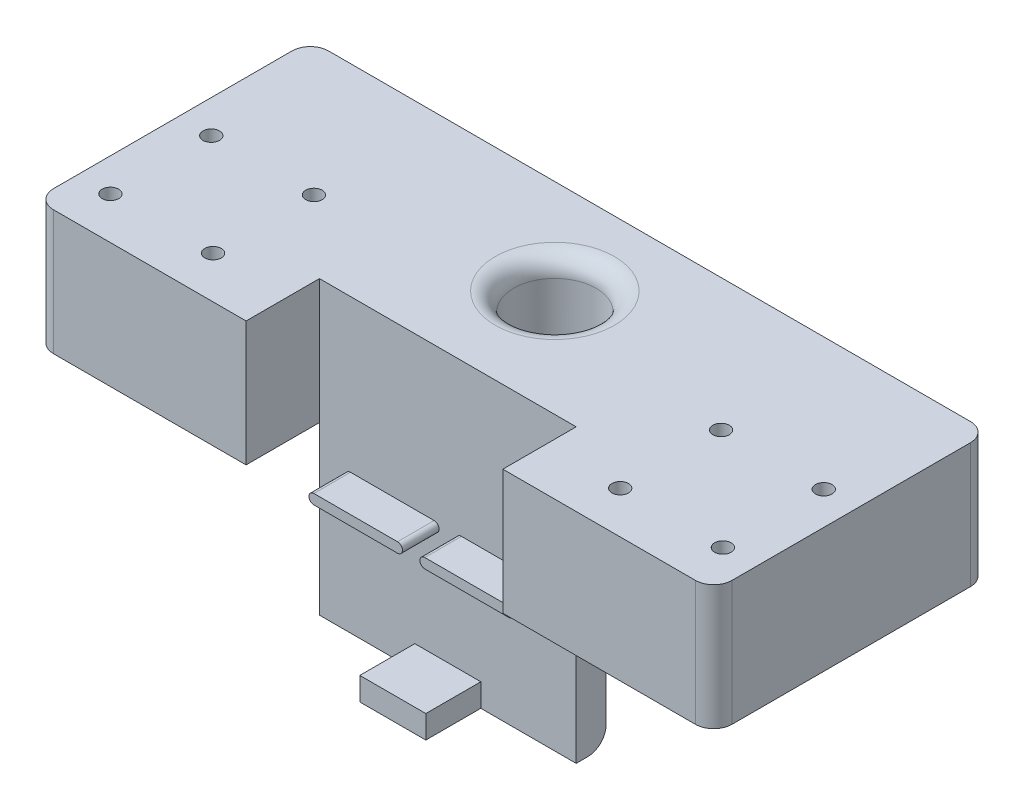
SolidWorks part; units mm, degrees
ref_plane "Front Plane" through (0, 0, 0) normal (0, 0, 1) x (1, 0, 0)
ref_plane "Top Plane" through (0, 0, 0) normal (0, 1, 0) x (1, 0, 0)
ref_plane "Right Plane" through (0, 0, 0) normal (1, 0, 0) x (0, 0, -1)
ref_plane "Plane1" through (0, -15, 0) normal (0, -1, 0) x (1, 0, 0)
sketch "Sketch1" plane through (0, -15, 0) normal (0, -1, 0) x (1, 0, 0)
  line L0 (-92.5, 0) -> (92.5, 0)
  line L1 (92.5, 0) -> (92.5, 55)
  line L2 (92.5, 55) -> (-92.5, 55)
  line L3 (-92.5, 55) -> (-92.5, 0)
extrude "Boss-Extrude1" add sketch "Sketch1" against normal blind 49
sketch "Sketch2" plane through (0, 0, 55) normal (0, 0, 1) x (1, 0, 0)
  line L0 (26.525, -10.2) -> (3.725, -10.2)
  line L1 (3.725, -7.5) -> (26.525, -7.5)
  line L2 (92.5, 34) -> (-92.5, 34) construction
  arc A0 (26.525, -7.5) -> (26.525, -10.2) centre (26.525, -8.85) cw
  arc A1 (3.725, -10.2) -> (3.725, -7.5) centre (3.725, -8.85) cw
  dimension "D1" = 41.5
extrude "Boss-Extrude2" add sketch "Sketch2" along normal blind 10
sketch "Sketch3" plane through (0, -10.2, 0) normal (0, -1, 0) x (1, 0, 0)
  line L0 (17.9948, 65) -> (0, 65)
  line L1 (0, 65) -> (0, 56.75)
  arc A0 (0, 56.75) -> (17.9948, 65) centre (0, 80.5) ccw
sketch "Sketch4" plane through (0, 0, 0) normal (0, 0, -1) x (-1, 0, 0)
  line L0 (-35, -15) -> (-35, 0)
  line L1 (-35, 0) -> (-92.5, 0)
  line L2 (-92.5, 0) -> (-92.5, -15)
  line L3 (-92.5, -15) -> (-35, -15)
extrude "Cut-Extrude2" cut sketch "Sketch4" against normal through all
sketch "Sketch5" plane through (0, 0, 55) normal (0, 0, 1) x (1, 0, 0)
  line L0 (-92.5, -15) -> (-35, -15)
  line L1 (-35, -15) -> (-35, 0)
  line L2 (-35, 0) -> (-92.5, 0)
  line L3 (-92.5, 0) -> (-92.5, -15)
extrude "Cut-Extrude3" cut sketch "Sketch5" against normal through all
sketch "Sketch6" plane through (0, 0, 55) normal (0, 0, 1) x (1, 0, 0)
  line L0 (-26.525, -7.5) -> (-3.725, -7.5)
  line L1 (-3.725, -10.2) -> (-26.525, -10.2)
  line L2 (92.5, 34) -> (-92.5, 34) construction
  arc A0 (-26.525, -10.2) -> (-26.525, -7.5) centre (-26.525, -8.85) cw
  arc A1 (-3.725, -7.5) -> (-3.725, -10.2) centre (-3.725, -8.85) cw
  dimension "D1" = 41.5
extrude "Boss-Extrude3" add sketch "Sketch6" along normal blind 10
sketch "Sketch7" plane through (0, -7.5, 0) normal (0, 1, 0) x (-1, 0, 0)
  line L0 (17.9948, 65) -> (-0.1994, 65)
  line L1 (-0.1994, 65) -> (-0.1994, 56.7508)
  arc A0 (-0.1994, 56.7508) -> (17.9948, 65) centre (0, 80.5) ccw
sketch "Sketch8" plane through (0, 0, 0) normal (0, 0, -1) x (-1, 0, 0)
  line L0 (-11.45, 16.55) -> (11.45, 16.55)
  line L1 (11.45, 13.95) -> (-11.45, 13.95)
  line L2 (92.5, 34) -> (-92.5, 34) construction
  line L3 (-35, -7.5) -> (35, -7.5) construction
  line L4 (-35, -15) -> (-35, 0) construction
  line L5 (35, -15) -> (35, 0) construction
  arc A0 (11.45, 16.55) -> (11.45, 13.95) centre (11.45, 15.25) cw
  arc A1 (-11.45, 13.95) -> (-11.45, 16.55) centre (-11.45, 15.25) cw
  dimension "D1" = 22.75
  dimension "D2" = 41.5
  dimension "D3" = 2.6
extrude "Boss-Extrude4" add sketch "Sketch8" along normal blind 3.5
sketch "Sketch10" plane through (0, 0, 0) normal (0, 0, -1) x (-1, 0, 0)
  line L0 (-18.55, 13.95) -> (-42.45, 13.95)
  line L1 (-42.45, 16.55) -> (-18.55, 16.55)
  line L2 (92.5, 34) -> (-92.5, 34) construction
  line L3 (0, 0) -> (0, 34) construction
  line L4 (42.45, 16.55) -> (18.55, 16.55)
  line L5 (18.55, 13.95) -> (42.45, 13.95)
  line L6 (-42.45, 16.55) -> (-43.75, 16.55) construction
  line L7 (-43.75, 16.55) -> (-43.75, 13.95) construction
  line L8 (-43.75, 13.95) -> (-42.45, 13.95) construction
  line L9 (-18.55, 16.55) -> (-17.25, 16.55) construction
  line L10 (-17.25, 16.55) -> (-17.25, 13.95) construction
  line L11 (-17.25, 13.95) -> (-18.55, 13.95) construction
  line L12 (-35, -7.5) -> (35, -7.5) construction
  line L13 (-35, -15) -> (-35, 0) construction
  line L14 (35, -15) -> (35, 0) construction
  arc A0 (-42.45, 13.95) -> (-42.45, 16.55) centre (-42.45, 15.25) cw
  arc A1 (-18.55, 16.55) -> (-18.55, 13.95) centre (-18.55, 15.25) cw
  arc A2 (18.55, 16.55) -> (18.55, 13.95) centre (18.55, 15.25) ccw
  arc A3 (42.45, 13.95) -> (42.45, 16.55) centre (42.45, 15.25) ccw
  dimension "D3" = 26.5
  dimension "D4" = 22.75
  dimension "D1" = 41.5
  dimension "D2" = 17.25
  dimension "D5" = 2.6
sketch "Sketch11" plane through (0, 0, 0) normal (0, 0, -1) x (-1, 0, 0)
  line L0 (-31, -3) -> (31, -3)
  line L1 (31, -7.5) -> (-31, -7.5)
  line L2 (92.5, 34) -> (-92.5, 34) construction
  line L3 (0, 34) -> (0, -15) construction
  line L4 (35, -15) -> (-35, -15) construction
  arc A0 (31, -3) -> (31, -7.5) centre (31, -5.25) cw
  arc A1 (-31, -7.5) -> (-31, -3) centre (-31, -5.25) cw
  point P12 (0, -7.5)
  dimension "D1" = 4.5
  dimension "D2" = 62
  dimension "D3" = 41.5
extrude "Boss-Extrude7" add sketch "Sketch11" along normal blind 3.5
extrude "Boss-Extrude8" add sketch "Sketch10" along normal blind 3.5
sketch "Sketch14" plane through (0, 0, 55) normal (0, 0, 1) x (1, 0, 0)
  line L0 (35, 0) -> (35, -15) construction
  line L1 (-35, -15) -> (35, -15)
  line L2 (-35, -15) -> (-35, -10.7362)
  line L3 (-35, -10.7362) -> (35, -10.7362)
  line L4 (35, -15) -> (35, -10.7362)
extrude "Cut-Extrude5" cut sketch "Sketch14" against normal through all
sketch "Sketch15" plane through (0, 0, 55) normal (0, 0, 1) x (1, 0, 0)
  line L1 (-92.5, 34) -> (-35, 34)
  line L2 (-92.5, 34) -> (-92.5, 0)
  line L3 (-92.5, 0) -> (-35, 0)
  line L4 (-35, 34) -> (-35, 0)
  line L5 (35, 0) -> (92.5, 0)
  line L6 (35, 0) -> (35, 34)
  line L7 (35, 34) -> (92.5, 34)
  line L8 (92.5, 0) -> (92.5, 34)
extrude "Boss-Extrude9" add sketch "Sketch15" along normal blind 20
sketch "Sketch17" plane through (0, 0, 0) normal (0, -1, 0) x (1, 0, 0)
  line L0 (-83.5, 63.5) -> (-55.5, 63.5) construction
  line L1 (-55.5, 63.5) -> (-55.5, 36) construction
  line L2 (-55.5, 36) -> (-83.5, 36) construction
  line L3 (-83.5, 36) -> (-83.5, 63.5) construction
  line L4 (-69.5, 63.5) -> (-69.5, 36) construction
  line L5 (0, 55) -> (0, 0) construction
  line L6 (69.5, 63.5) -> (69.5, 36) construction
  line L7 (83.5, 36) -> (83.5, 63.5) construction
  line L8 (55.5, 36) -> (83.5, 36) construction
  line L9 (55.5, 63.5) -> (55.5, 36) construction
  line L10 (83.5, 63.5) -> (55.5, 63.5) construction
  line L11 (35, 55) -> (-35, 55) construction
  line L13 (-92.5, 75) -> (-35, 75) construction
  point P0 (-55.5, 63.5)
  point P1 (-83.5, 63.5)
  point P2 (-83.5, 36)
  point P3 (-55.5, 36)
  point P18 (55.5, 36)
  point P19 (83.5, 36)
  point P20 (83.5, 63.5)
  point P21 (55.5, 63.5)
  dimension "D1" = 27.5
  dimension "D2" = 28
  dimension "D3" = 69.5
  dimension "D4" = 11.5
hole_wizard "CBORE for M4 Pan Head Machine Screw1" positions "Sketch17" profile "Sketch18" counterbore size "M4" standard "ANSI Metric" end condition through all
sketch "Sketch18" plane through (-55.5, 0, 63.5) normal (1, 0, 0) x (0, 0, -1)
  line L0 (0, 0) -> (0, 34)
  line L1 (0, 34) -> (2.25, 34)
  line L3 (2.25, 34) -> (2.25, 3.1)
  line L4 (2.25, 3.1) -> (4.5, 3.1)
  line L5 (4.5, 3.1) -> (4.5, 0)
  line L7 (4.5, 0) -> (0, 0)
  line L11 (0, -6.35) -> (0, 107.95) construction
  dimension "Thru Hole Dia." = 4.5
  dimension "Thru Hole Depth" = 34
  dimension "C'Bore Dia." = 9
  dimension "C'Bore Depth" = 3.1
sketch "Sketch19" plane through (0, -10.7362, 0) normal (0, -1, 0) x (1, 0, 0)
  line L0 (35, 0) -> (35, 55) construction
  line L1 (-35, 55) -> (35, 55)
  line L2 (-35, 55) -> (-35, 46.854)
  line L3 (-35, 46.854) -> (35, 46.854)
  line L4 (35, 55) -> (35, 46.854)
extrude "Boss-Extrude10" add sketch "Sketch19" along normal blind 34.74
sketch "Sketch20" plane through (0, 0, 55) normal (0, 0, 1) x (1, 0, 0)
  line L1 (-9, -45.4719) -> (9, -45.4719)
  line L2 (-9, -45.4719) -> (-9, -39.2)
  line L3 (-9, -39.2) -> (9, -39.2)
  line L4 (9, -45.4719) -> (9, -39.2)
  line L5 (-26.525, -10.2) -> (-3.725, -10.2) construction
  point P4 (0, -39.2)
  dimension "D1" = 18
  dimension "D2" = 29
extrude "Boss-Extrude11" add sketch "Sketch20" along normal blind 15
fillet "Fillet1" radius 5 5 edges at (0, -45.4762, 46.854) (-92.5, 17, 75) (-92.5, 17, 0) (92.5, 17, 0) (92.5, 17, 75)
sketch "Sketch21" plane through (0, 34, 0) normal (0, 1, 0) x (1, 0, 0)
  circle A0 centre (0, -25.818) radius 11.25
  dimension "D1" = 22.5
extrude "Cut-Extrude6" cut sketch "Sketch21" against normal through all
fillet "Fillet2" radius 5 1 edges at (0, 34, 37.068)
sketch "Sketch22" plane through (0, 0, 55) normal (0, 0, 1) x (1, 0, 0)
  line L0 (-9, -39.2) -> (-9, -45.4719) construction
  line L1 (-9, -45.4719) -> (9, -45.4719) construction
  line L2 (9, -45.4719) -> (9, -39.2) construction
  line L3 (9, -39.2) -> (-9, -39.2) construction
  line L4 (26.525, -7.5) -> (3.725, -7.5) construction
  line L5 (3.725, -10.2) -> (26.525, -10.2) construction
  line L6 (-26.525, -10.2) -> (-3.725, -10.2) construction
  line L7 (-3.725, -7.5) -> (-26.525, -7.5) construction
  line L8 (-9, -39.2) -> (-9, -45.4719)
  line L9 (-9, -45.4719) -> (9, -45.4719)
  line L10 (9, -45.4719) -> (9, -39.2)
  line L11 (9, -39.2) -> (-9, -39.2)
  line L12 (26.525, -7.5) -> (3.725, -7.5)
  line L13 (3.725, -10.2) -> (26.525, -10.2)
  line L14 (-26.525, -10.2) -> (-3.725, -10.2)
  line L15 (-3.725, -7.5) -> (-26.525, -7.5)
  arc A0 (26.525, -10.2) -> (26.525, -7.5) centre (26.525, -8.85) ccw construction
  arc A1 (3.725, -7.5) -> (3.725, -10.2) centre (3.725, -8.85) ccw construction
  arc A2 (-26.525, -7.5) -> (-26.525, -10.2) centre (-26.525, -8.85) ccw construction
  arc A3 (-3.725, -10.2) -> (-3.725, -7.5) centre (-3.725, -8.85) ccw construction
  arc A4 (26.525, -10.2) -> (26.525, -7.5) centre (26.525, -8.85) ccw
  arc A5 (3.725, -7.5) -> (3.725, -10.2) centre (3.725, -8.85) ccw
  arc A6 (-26.525, -7.5) -> (-26.525, -10.2) centre (-26.525, -8.85) ccw
  arc A7 (-3.725, -10.2) -> (-3.725, -7.5) centre (-3.725, -8.85) ccw
